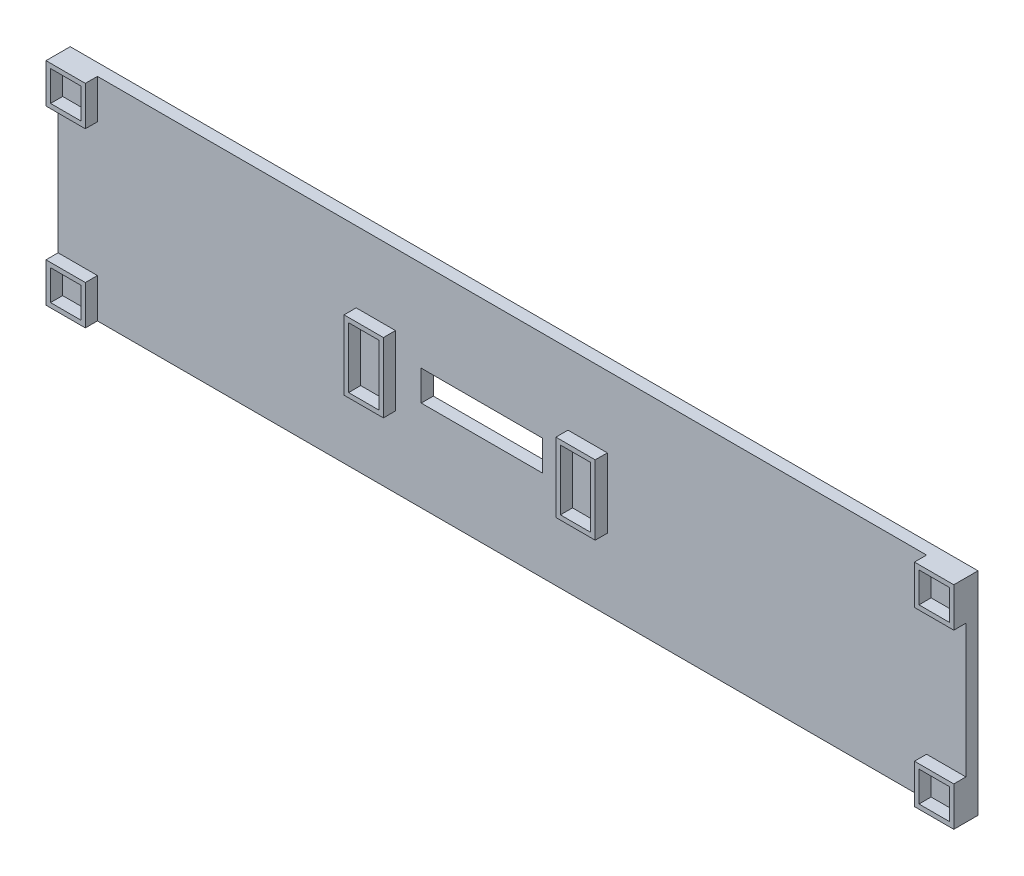
SolidWorks part; units mm, degrees
ref_plane "Přední rovina" through (0, 0, 0) normal (0, 0, 1) x (1, 0, 0)
ref_plane "Horní rovina" through (0, 0, 0) normal (0, 1, 0) x (1, 0, 0)
ref_plane "Pravá rovina" through (0, 0, 0) normal (1, 0, 0) x (0, 0, -1)
sketch "Skica1" plane through (0, 0, 0) normal (0, 0, 1) x (1, 0, 0)
  line L1 (75, 17.5) -> (-75, 17.5)
  line L2 (75, 17.5) -> (75, -17.5)
  line L3 (75, -17.5) -> (-75, -17.5)
  line L4 (-75, 17.5) -> (-75, -17.5)
  line L5 (75, 17.5) -> (-75, -17.5) construction
  line L6 (75, -17.5) -> (-75, 17.5) construction
  point P0 (0, 0)
  point P5 (-27.5, 0)
  point P11 (4.5, 0)
  dimension "D1" = 35
  dimension "D2" = 150
extrude "Přidat vysunutím2" add sketch "Skica1" along normal blind 2 contours L2 L1 L4 L3
sketch "Skica2" plane through (0, 0, 2) normal (0, 0, 1) x (1, 0, 0)
  line L0 (-75, 17.5) -> (-75, -17.5) construction
  line L1 (-25, 5) -> (-20, 5)
  line L2 (-25, 5) -> (-25, -5)
  line L3 (-25, -5) -> (-20, -5)
  line L4 (-20, 5) -> (-20, -5)
  line L5 (-25, 5) -> (-20, -5) construction
  line L6 (-25, -5) -> (-20, 5) construction
  line L8 (15, 5) -> (10, 5)
  line L9 (15, 5) -> (15, -5)
  line L10 (15, -5) -> (10, -5)
  line L11 (10, 5) -> (10, -5)
  line L12 (15, 5) -> (10, -5) construction
  line L13 (15, -5) -> (10, 5) construction
  line L14 (-25.75, 5.75) -> (-19.25, 5.75)
  line L15 (-25.75, 5.75) -> (-25.75, -5.75)
  line L16 (-25.75, -5.75) -> (-19.25, -5.75)
  line L17 (-19.25, 5.75) -> (-19.25, -5.75)
  line L18 (-25.75, 5.75) -> (-19.25, -5.75) construction
  line L19 (-25.75, -5.75) -> (-19.25, 5.75) construction
  line L20 (9.25, 5.75) -> (15.75, 5.75)
  line L21 (9.25, 5.75) -> (9.25, -5.75)
  line L22 (9.25, -5.75) -> (15.75, -5.75)
  line L23 (15.75, 5.75) -> (15.75, -5.75)
  line L24 (9.25, 5.75) -> (15.75, -5.75) construction
  line L25 (9.25, -5.75) -> (15.75, 5.75) construction
  point P0 (-22.5, 0)
  point P7 (12.5, 0)
  point P12 (-22.5, 0)
  point P17 (12.5, 0)
  dimension "D1" = 10
  dimension "D2" = 5
  dimension "D3" = 50
  dimension "D4" = 10
  dimension "D5" = 5
  dimension "D6" = 30
  dimension "D7" = 11.5
  dimension "D8" = 6.5
  dimension "D9" = 11.5
  dimension "D10" = 6.5
extrude "Přidat vysunutím3" add sketch "Skica2" along normal blind 2
sketch "Skica3" plane through (0, 0, 2) normal (0, 0, 1) x (1, 0, 0)
  line L0 (75, 17.5) -> (-75, 17.5) construction
  line L1 (-75, 17.5) -> (-68.5, 17.5)
  line L2 (-75, 17.5) -> (-75, 11)
  line L3 (-75, 11) -> (-68.5, 11)
  line L4 (-68.5, 17.5) -> (-68.5, 11)
  line L5 (-75, 17.5) -> (-68.5, 11) construction
  line L6 (-75, 11) -> (-68.5, 17.5) construction
  line L7 (-75, 17.5) -> (-75, -17.5) construction
  line L8 (69.25, 16.75) -> (74.25, 11.75) construction
  line L9 (-74.25, 16.75) -> (-69.25, 16.75)
  line L10 (-74.25, 16.75) -> (-74.25, 11.75)
  line L11 (-74.25, 11.75) -> (-69.25, 11.75)
  line L12 (-69.25, 16.75) -> (-69.25, 11.75)
  line L13 (-74.25, 16.75) -> (-69.25, 11.75) construction
  line L14 (-74.25, 11.75) -> (-69.25, 16.75) construction
  line L15 (69.25, 11.75) -> (74.25, 16.75) construction
  line L16 (69.25, 16.75) -> (69.25, 11.75)
  line L17 (69.25, 16.75) -> (74.25, 16.75)
  line L18 (74.25, 16.75) -> (74.25, 11.75)
  line L19 (69.25, 11.75) -> (74.25, 11.75)
  line L20 (68.5, 17.5) -> (68.5, 11)
  line L21 (68.5, 17.5) -> (75, 17.5)
  line L22 (75, 17.5) -> (75, 11)
  line L23 (68.5, 11) -> (75, 11)
  line L24 (-74.25, -11.75) -> (-74.25, -16.75)
  line L25 (-74.25, -11.75) -> (-69.25, -11.75)
  line L26 (-69.25, -11.75) -> (-69.25, -16.75)
  line L27 (-74.25, -16.75) -> (-69.25, -16.75)
  line L28 (-75, -11) -> (-75, -17.5)
  line L29 (-75, -11) -> (-68.5, -11)
  line L30 (-68.5, -11) -> (-68.5, -17.5)
  line L31 (-75, -17.5) -> (-68.5, -17.5)
  line L32 (69.25, -11.75) -> (69.25, -16.75)
  line L33 (69.25, -16.75) -> (74.25, -16.75)
  line L34 (74.25, -11.75) -> (74.25, -16.75)
  line L35 (69.25, -11.75) -> (74.25, -11.75)
  line L36 (68.5, -11) -> (68.5, -17.5)
  line L37 (68.5, -17.5) -> (75, -17.5)
  line L38 (75, -11) -> (75, -17.5)
  line L39 (68.5, -11) -> (75, -11)
  point P0 (-71.75, 14.25)
  point P9 (-71.75, 14.25)
  point P20 (71.75, 14.25)
  dimension "D1" = 6.5
  dimension "D2" = 6.5
  dimension "D3" = 0
  dimension "D4" = 0
  dimension "D5" = 5
  dimension "D6" = 2
  dimension "D7" = 2
extrude "Přidat vysunutím4" add sketch "Skica3" along normal blind 2
sketch "Skica4" plane through (0, 0, 2) normal (0, 0, 1) x (1, 0, 0)
  line L0 (-19.25, -5.75) -> (-19.25, 5.75) construction
  line L1 (-15, 2.5) -> (5, 2.5)
  line L2 (-15, 2.5) -> (-15, -2.5)
  line L3 (-15, -2.5) -> (5, -2.5)
  line L4 (5, 2.5) -> (5, -2.5)
  line L5 (-15, 2.5) -> (5, -2.5) construction
  line L6 (-15, -2.5) -> (5, 2.5) construction
  line L7 (9.25, 5.75) -> (9.25, -5.75) construction
  point P0 (-5, 0)
  point P7 (-19.25, 0)
  dimension "D1" = 5
  dimension "D2" = 20
  dimension "D3" = 4.25
  dimension "D4" = 4.25
extrude "Odebrat vysunutím1" cut sketch "Skica4" against normal blind 2
